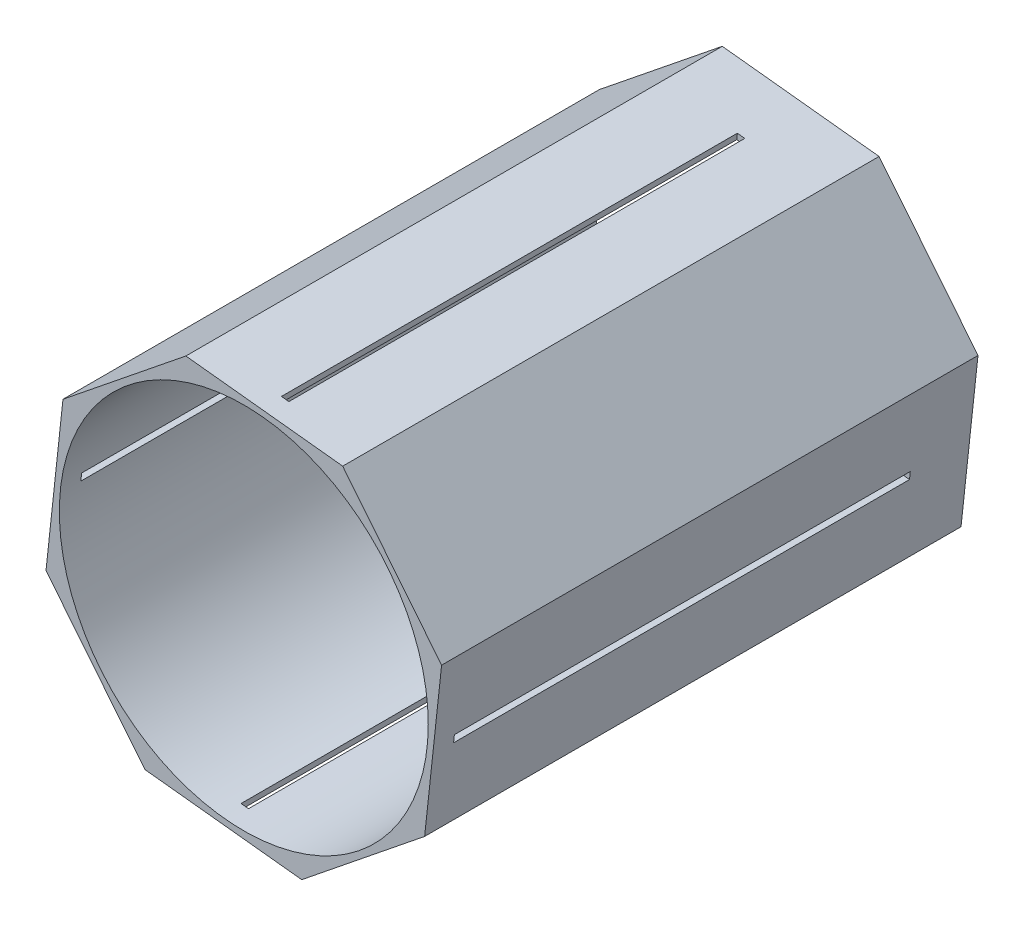
SolidWorks part; units mm, degrees
ref_plane "Front Plane" through (0, 0, 0) normal (0, 0, 1) x (1, 0, 0)
ref_plane "Top Plane" through (0, 0, 0) normal (0, 1, 0) x (1, 0, 0)
ref_plane "Right Plane" through (0, 0, 0) normal (1, 0, 0) x (0, 0, -1)
sketch "Sketch1" plane through (0, 0, 0) normal (0, 0, 1) x (1, 0, 0)
  line L0 (77.0666, -42.1485) -> (84.2978, 24.6908)
  line L1 (42.1485, 77.0666) -> (-24.6908, 84.2978)
  line L2 (-24.6908, 84.2978) -> (-77.0666, 42.1485)
  line L3 (-77.0666, 42.1485) -> (-84.2978, -24.6908)
  line L4 (-84.2978, -24.6908) -> (-42.1485, -77.0666)
  line L5 (-42.1485, -77.0666) -> (24.6908, -84.2978)
  line L6 (24.6908, -84.2978) -> (77.0666, -42.1485)
  line L7 (84.2978, 24.6908) -> (42.1485, 77.0666)
  circle A0 centre (0, 0) radius 78.613
  circle A1 centre (0, 0) radius 81.153 construction
  dimension "D1" = 157.226
  dimension "D2" = 2.54
extrude "Boss-Extrude1" add sketch "Sketch1" along normal blind 228.6
sketch "Sketch2" plane through (8.7288, 80.6822, 0) normal (0.1076, 0.9942, 0) x (0.9942, -0.1076, 0)
  line L0 (0, 0) -> (0, -228.6) construction
  line L1 (33.6147, -228.6) -> (-33.6147, -228.6) construction
  line L3 (-1.5875, -25.4) -> (1.5875, -25.4)
  line L4 (-1.5875, -25.4) -> (-1.5875, -219.71)
  line L5 (-1.5875, -219.71) -> (1.5875, -219.71)
  line L6 (1.5875, -25.4) -> (1.5875, -219.71)
  line L7 (-1.5875, -25.4) -> (1.5875, -219.71) construction
  line L8 (-1.5875, -219.71) -> (1.5875, -25.4) construction
  point P5 (0, -122.555)
  point P10 (0, -219.71)
  dimension "D1" = 8.89
  dimension "D2" = 3.175
  dimension "D3" = 194.31
extrude "Cut-Extrude1" cut sketch "Sketch2" against normal blind 203.2
sketch "Sketch5" plane through (-80.6822, 8.7288, 0) normal (-0.9942, 0.1076, 0) x (0, 0, 1)
  line L0 (0, 0) -> (228.6, 0) construction
  line L1 (0, 33.6147) -> (0, -33.6147) construction
  line L2 (228.6, 33.6147) -> (228.6, -33.6147) construction
  line L4 (25.4, -1.5875) -> (219.71, -1.5875)
  line L5 (25.4, -1.5875) -> (25.4, 1.5875)
  line L6 (25.4, 1.5875) -> (219.71, 1.5875)
  line L7 (219.71, -1.5875) -> (219.71, 1.5875)
  line L8 (25.4, -1.5875) -> (219.71, 1.5875) construction
  line L9 (25.4, 1.5875) -> (219.71, -1.5875) construction
  point P6 (122.555, 0)
  point P11 (219.71, 0)
  dimension "D1" = 8.89
  dimension "D2" = 3.175
  dimension "D3" = 194.31
extrude "Cut-Extrude2" cut sketch "Sketch5" against normal blind 203.2
